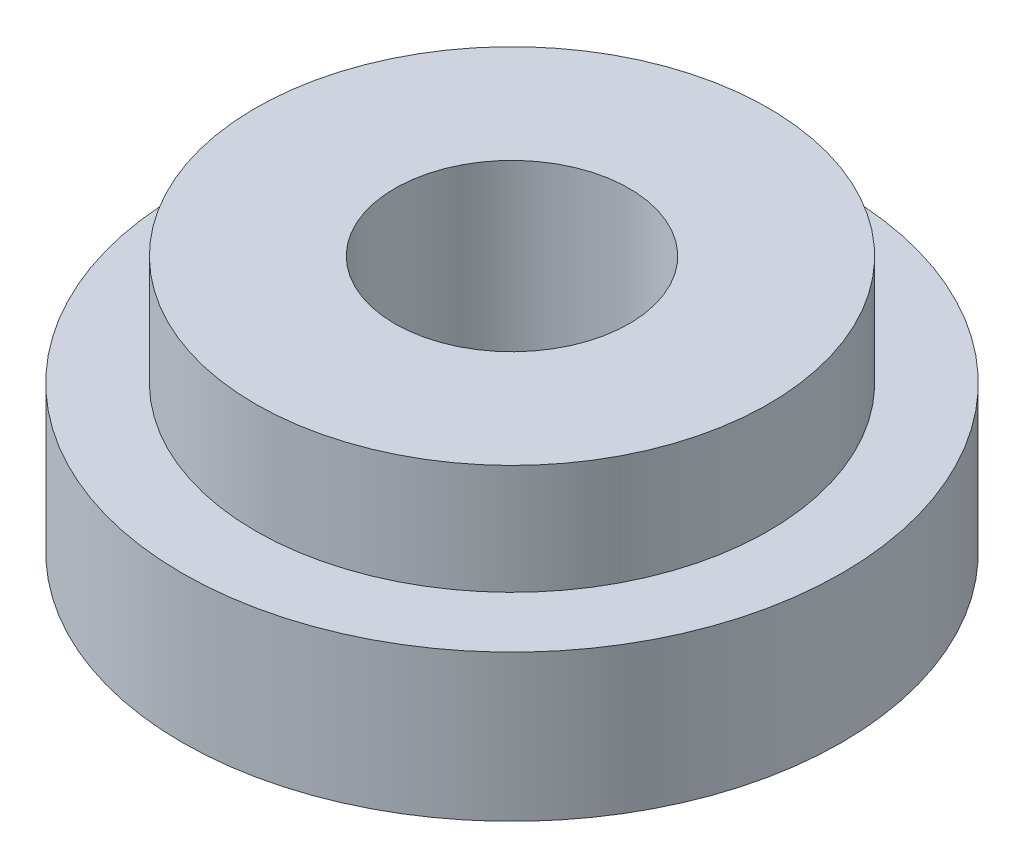
SolidWorks part; units mm, degrees
ref_plane "Front Plane" through (0, 0, 0) normal (0, 0, 1) x (1, 0, 0)
ref_plane "Top Plane" through (0, 0, 0) normal (0, 1, 0) x (1, 0, 0)
ref_plane "Right Plane" through (0, 0, 0) normal (1, 0, 0) x (0, 0, -1)
sketch "Sketch1" plane through (0, 0, 0) normal (0, 1, 0) x (1, 0, 0)
  circle A0 centre (0, 0) radius 4.5
  dimension "D1" = 9
extrude "Boss-Extrude1" add sketch "Sketch1" along normal blind 2
sketch "Sketch2" plane through (0, 2, 0) normal (0, 1, 0) x (1, 0, 0)
  circle A0 centre (0, 0) radius 3.5
  dimension "D1" = 7
extrude "Boss-Extrude2" add sketch "Sketch2" along normal blind 1.5
sketch "Sketch3" plane through (0, 3.5, 0) normal (0, 1, 0) x (1, 0, 0)
  circle A0 centre (0, 0) radius 1.6
  dimension "D1" = 3.2
extrude "Cut-Extrude1" cut sketch "Sketch3" against normal through all
